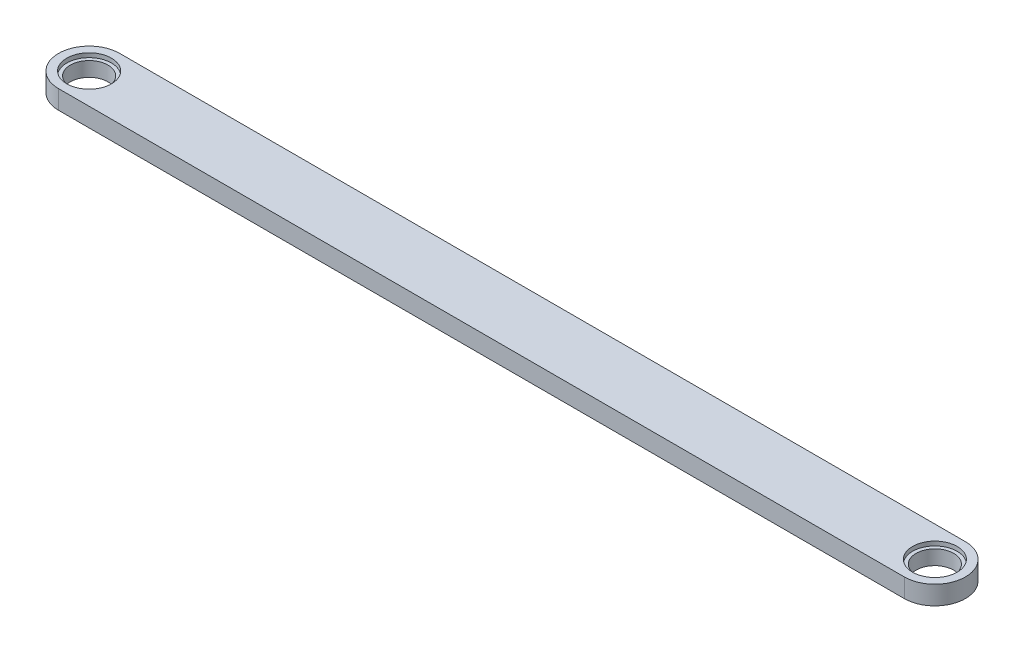
SolidWorks part; units mm, degrees
ref_plane "前视基准面" through (0, 0, 0) normal (0, 0, 1) x (1, 0, 0)
ref_plane "上视基准面" through (0, 0, 0) normal (0, 1, 0) x (1, 0, 0)
ref_plane "右视基准面" through (0, 0, 0) normal (1, 0, 0) x (0, 0, -1)
other "Configuration Table"
sketch "草图1" plane through (0, 0, 0) normal (0, 1, 0) x (1, 0, 0)
  line L0 (0, 0) -> (180, 0) construction
  line L1 (0, 6.5) -> (180, 6.5)
  line L2 (0, -6.5) -> (180, -6.5)
  arc A0 (0, 6.5) -> (0, -6.5) centre (0, 0) ccw
  arc A1 (180, -6.5) -> (180, 6.5) centre (180, 0) ccw
  point P3 (90, 0)
  dimension "D2" = 6.5
  dimension "D1" = 180
extrude "凸台-拉伸1" add sketch "草图1" along normal blind 4
sketch "草图3" plane through (0, 4, 0) normal (0, 1, 0) x (1, 0, 0)
  point P0 (180, 0)
  point P4 (0, 0)
hole_wizard "M5 六角头螺栓的柱形沉头孔1" positions "草图3" profile "草图4" counterbore size "M5" standard "GB" end condition through all
sketch "草图4" plane through (180, 4, 0) normal (1, 0, 0) x (0, 0, 1)
  line L0 (0, 0) -> (0, 4)
  line L1 (0, 4) -> (4, 4)
  line L3 (4, 4) -> (4, 0.9)
  line L4 (4, 0.9) -> (4.75, 0.9)
  line L5 (4.75, 0.9) -> (4.75, 0)
  line L7 (4.75, 0) -> (0, 0)
  line L11 (0, -6.35) -> (0, 107.95) construction
  dimension "通孔孔直径" = 8
  dimension "通孔孔深度" = 4
  dimension "柱形沉头孔直径" = 9.5
  dimension "柱形沉头孔深度" = 0.9
